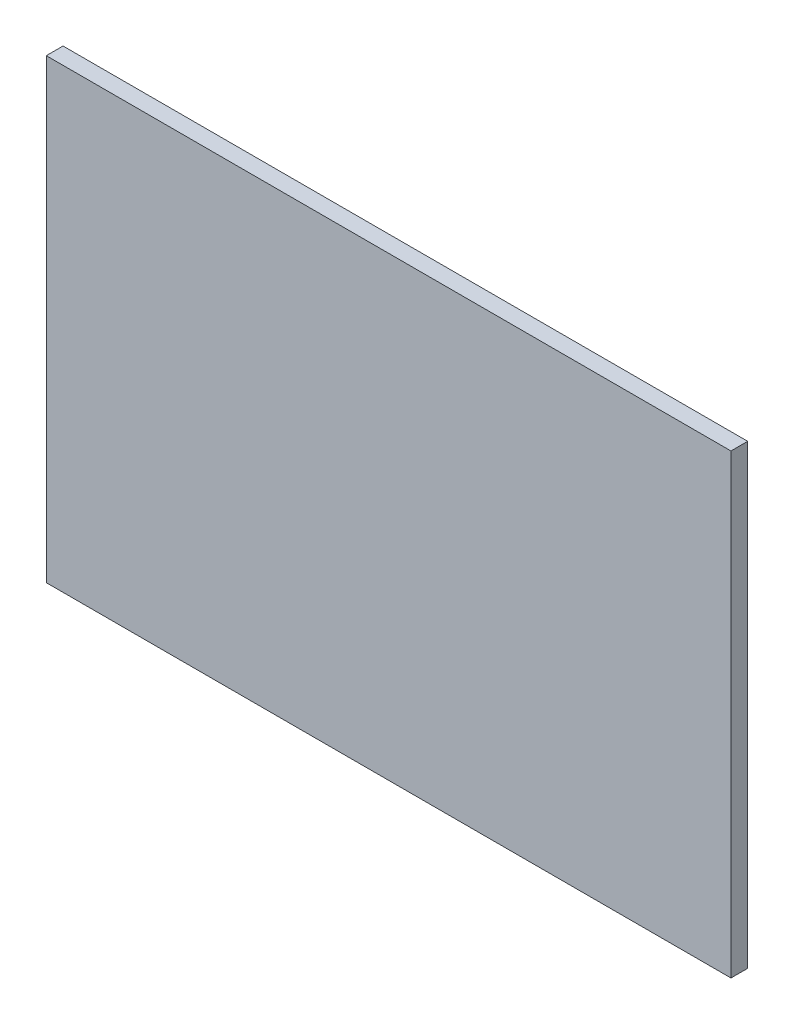
SolidWorks part; units mm, degrees
ref_plane "前视基准面" through (0, 0, 0) normal (0, 0, 1) x (1, 0, 0)
ref_plane "上视基准面" through (0, 0, 0) normal (0, 1, 0) x (1, 0, 0)
ref_plane "右视基准面" through (0, 0, 0) normal (1, 0, 0) x (0, 0, -1)
sketch "草图1" plane through (0, 0, 0) normal (0, 0, 1) x (1, 0, 0)
  line L1 (-22.5, -15) -> (22.5, -15)
  line L2 (-22.5, -15) -> (-22.5, 15)
  line L3 (-22.5, 15) -> (22.5, 15)
  line L4 (22.5, -15) -> (22.5, 15)
  line L5 (-22.5, -15) -> (22.5, 15) construction
  line L6 (-22.5, 15) -> (22.5, -15) construction
  circle A0 centre (0, 0) radius 8.75 construction
  dimension "D1" = 17.5
  dimension "D2" = 30
  dimension "D3" = 45
extrude "凸台-拉伸1" add sketch "草图1" along normal blind 1.1
